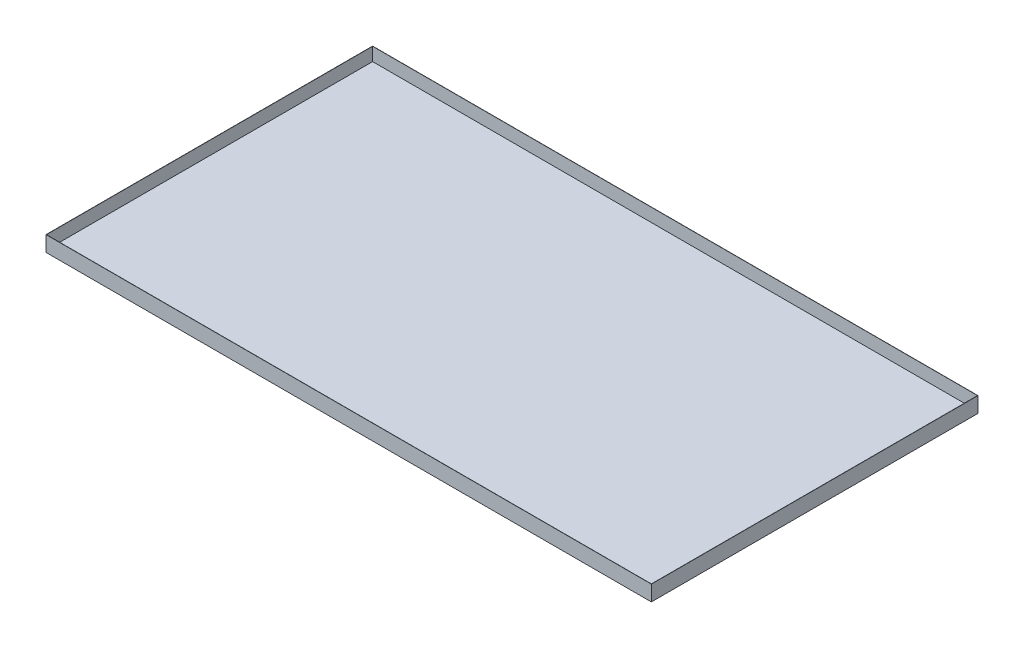
SolidWorks part; units mm, degrees
ref_plane "前视基准面" through (0, 0, 0) normal (0, 0, 1) x (1, 0, 0)
ref_plane "上视基准面" through (0, 0, 0) normal (0, 1, 0) x (1, 0, 0)
ref_plane "右视基准面" through (0, 0, 0) normal (1, 0, 0) x (0, 0, -1)
sketch "草图1" plane through (0, 0, 0) normal (0, 1, 0) x (1, 0, 0)
  line L1 (-13910, 7500) -> (13910, 7500)
  line L2 (-13910, 7500) -> (-13910, -7500)
  line L3 (-13910, -7500) -> (13910, -7500)
  line L4 (13910, 7500) -> (13910, -7500)
  line L5 (0, -7500) -> (0, 7500) construction
  line L6 (-13910, 0) -> (13910, 0) construction
  point P0 (0, 0)
  dimension "D1" = 27820
  dimension "D2" = 15000
extrude "凸台-拉伸1" add sketch "草图1" along normal blind 100
sketch "草图2" plane through (0, 100, 0) normal (0, 1, 0) x (1, 0, 0)
  circle A0 centre (0, 0) radius 500
  dimension "D1" = 1000
sketch "草图3" plane through (-13910, 0, 0) normal (-1, 0, 0) x (0, 0, 1)
  line L1 (-7500, 0) -> (7500, 0)
  line L2 (-7500, 0) -> (-7500, 710)
  line L3 (-7500, 710) -> (7500, 710)
  line L4 (7500, 0) -> (7500, 710)
  dimension "D1" = 710
extrude "凸台-拉伸2" add sketch "草图3" along normal blind 10
sketch "草图4" plane through (0, 0, 7500) normal (0, 0, 1) x (1, 0, 0)
  line L0 (-13920, 710) -> (-13910, 710) construction
  line L1 (-13920, 0) -> (13910, 0)
  line L2 (-13920, 0) -> (-13920, 710)
  line L3 (-13920, 710) -> (13910, 710)
  line L4 (13910, 0) -> (13910, 710)
extrude "凸台-拉伸3" add sketch "草图4" along normal blind 10
sketch "草图5" plane through (13910, 0, 0) normal (1, 0, 0) x (0, 0, -1)
  line L1 (-7510, 0) -> (7500, 0)
  line L2 (-7510, 0) -> (-7510, 710)
  line L3 (-7510, 710) -> (7500, 710)
  line L4 (7500, 0) -> (7500, 710)
extrude "凸台-拉伸4" add sketch "草图5" along normal blind 10
sketch "草图7" plane through (0, 0, -7500) normal (0, 0, -1) x (-1, 0, 0)
  line L1 (-13920, 0) -> (13920, 0)
  line L2 (-13920, 0) -> (-13920, 710)
  line L3 (-13920, 710) -> (13920, 710)
  line L4 (13920, 0) -> (13920, 710)
extrude "凸台-拉伸6" add sketch "草图7" along normal blind 10
